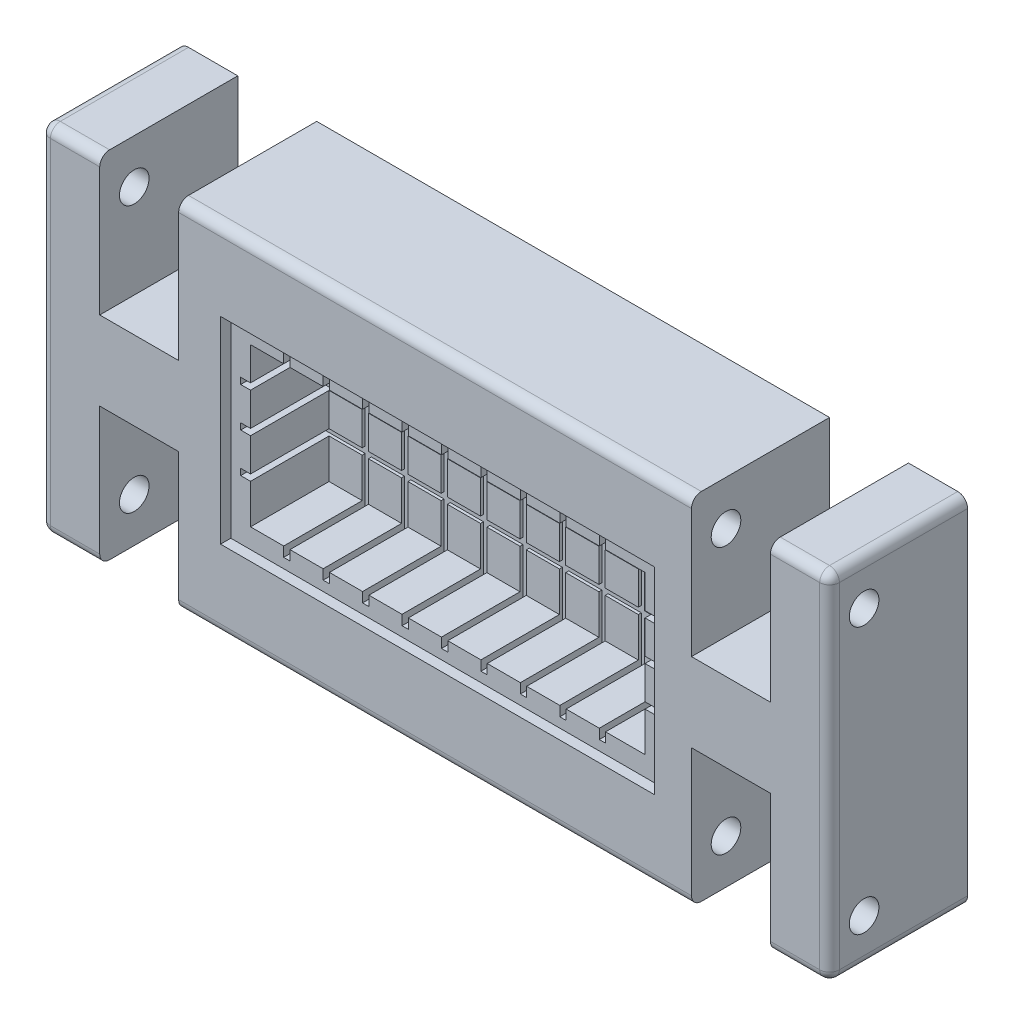
SolidWorks part; units mm, degrees
ref_plane "Alzado" through (0, 0, 0) normal (0, 0, 1) x (1, 0, 0)
ref_plane "Planta" through (0, 0, 0) normal (0, 1, 0) x (1, 0, 0)
ref_plane "Vista lateral" through (0, 0, 0) normal (1, 0, 0) x (0, 0, -1)
sketch "Croquis2" plane through (0, 0, 0) normal (0, 0, 1) x (1, 0, 0)
  line L1 (0, 0) -> (400, 0)
  line L2 (0, 0) -> (0, 180)
  line L3 (0, 180) -> (400, 180)
  line L4 (400, 0) -> (400, 180)
  dimension "D1" = 400
  dimension "D2" = 180
extrude "Saliente-Extruir3" add sketch "Croquis2" along normal blind 70
sketch "Croquis3" plane through (0, 0, 70) normal (0, 0, 1) x (1, 0, 0)
  line L0 (0, 90) -> (400, 90)
  line L1 (0, 180) -> (0, 0) construction
  line L2 (400, 0) -> (400, 180) construction
  line L3 (0, 0) -> (400, 0) construction
  line L4 (30, 0) -> (70, 0)
  line L5 (30, 0) -> (30, 70)
  line L6 (30, 70) -> (70, 70)
  line L7 (70, 0) -> (70, 70)
  line L8 (30, 0) -> (0, 0)
  line L9 (200, 90) -> (200, 0)
  line L10 (370, 0) -> (400, 0)
  line L11 (330, 0) -> (330, 70)
  line L12 (370, 70) -> (330, 70)
  line L13 (370, 0) -> (370, 70)
  line L14 (370, 0) -> (330, 0)
  line L15 (370, 180) -> (330, 180)
  line L16 (370, 180) -> (370, 110)
  line L17 (370, 110) -> (330, 110)
  line L18 (330, 180) -> (330, 110)
  line L19 (370, 180) -> (400, 180)
  line L20 (30, 180) -> (0, 180)
  line L21 (70, 180) -> (70, 110)
  line L22 (30, 110) -> (70, 110)
  line L23 (30, 180) -> (30, 110)
  line L24 (30, 180) -> (70, 180)
  line M9 (0, 0) -> (400, 0)
  line M11 (400, 180) -> (0, 180)
  dimension "D1" = 40
  dimension "D2" = 70
  dimension "D3" = 30
extrude "Cortar-Extruir1" cut sketch "Croquis3" against normal blind 70 contours L23 L22 L21 M11 | L13 L12 L11 M9 | L7 L6 L5 M9 | L16 L17 L18 L15
sketch "Croquis4" plane through (400, 0, 0) normal (1, 0, 0) x (0, 0, -1)
  line L0 (-70, 180) -> (-35, 135) construction
  line L1 (-70, 180) -> (-35, 180) construction
  line L2 (-70, 180) -> (-70, 135) construction
  line L3 (-70, 135) -> (-35, 135) construction
  line L4 (-35, 180) -> (-35, 135) construction
  line L5 (0, 90) -> (-70, 90) construction
  line L6 (0, 0) -> (0, 180) construction
  line L7 (-70, 0) -> (-70, 180) construction
  circle A0 centre (-52.5, 157.5) radius 7.5
  circle A1 centre (-52.5, 22.5) radius 7.5
  dimension "D3" = 15
  dimension "D1" = 45
  dimension "D2" = 35
extrude "Cortar-Extruir2" cut sketch "Croquis4" against normal blind 400
fillet "Redondeo2" radius 5 1 edges at (200, 0, 70)
fillet "Redondeo3" radius 5 1 edges at (200, 180, 70)
fillet "Redondeo4" radius 5 1 edges at (15, 180, 70)
fillet "Redondeo5" radius 5 1 edges at (385, 180, 70)
fillet "Redondeo6" radius 5 1 edges at (385, 0, 70)
fillet "Redondeo7" radius 5 1 edges at (15, 0, 70)
fillet "Redondeo8" radius 5 5 edges at (0, 90, 70) (0, 180, 32.5) (0, 178.5355, 68.5355) (0, 0, 32.5) (0, 1.4645, 68.5355)
fillet "Redondeo9" radius 5 5 edges at (400, 180, 32.5) (400, 178.5355, 68.5355) (400, 90, 70) (400, 0, 32.5) (400, 1.4645, 68.5355)
sketch "Croquis6" plane through (0, 0, 70) normal (0, 0, 1) x (1, 0, 0)
  line L4 (301.25, 130) -> (101.25, 130)
  line L5 (301.25, 130) -> (301.25, 50)
  line L6 (301.25, 50) -> (101.25, 50)
  line L7 (101.25, 130) -> (101.25, 50)
  line L8 (301.25, 130) -> (101.25, 50) construction
  line L9 (301.25, 50) -> (101.25, 130) construction
  point P9 (201.25, 90)
extrude "Cortar-Extruir3" cut sketch "Croquis6" against normal blind 45
sketch "Croquis7" plane through (0, 0, 70) normal (0, 0, 1) x (1, 0, 0)
  line L2 (241.25, 45) -> (238.05, 45)
  line L3 (241.25, 45) -> (241.25, 135)
  line L4 (138.05, 45) -> (141.25, 45)
  line L5 (138.05, 45) -> (138.05, 135)
  line L6 (118.05, 45) -> (121.25, 45)
  line L7 (118.05, 45) -> (118.05, 135)
  line L8 (118.05, 135) -> (121.25, 135)
  line L9 (121.25, 45) -> (121.25, 135)
  line L10 (118.05, 45) -> (121.25, 135) construction
  line L11 (118.05, 135) -> (121.25, 45) construction
  line L12 (138.05, 135) -> (141.25, 135)
  line L13 (141.25, 45) -> (141.25, 135)
  line L14 (138.05, 45) -> (141.25, 135) construction
  line L15 (138.05, 135) -> (141.25, 45) construction
  line L16 (241.25, 135) -> (238.05, 135)
  line L21 (238.05, 45) -> (238.05, 135)
  line L22 (158.05, 45) -> (161.25, 45)
  line L23 (158.05, 45) -> (158.05, 135)
  line L24 (158.05, 135) -> (161.25, 135)
  line L25 (161.25, 45) -> (161.25, 135)
  line L26 (158.05, 45) -> (161.25, 135) construction
  line L27 (158.05, 135) -> (161.25, 45) construction
  line L28 (241.25, 45) -> (238.05, 135) construction
  line L33 (241.25, 135) -> (238.05, 45) construction
  line L34 (178.05, 45) -> (181.25, 45)
  line L35 (178.05, 45) -> (178.05, 135)
  line L36 (178.05, 135) -> (181.25, 135)
  line L37 (181.25, 45) -> (181.25, 135)
  line L38 (178.05, 45) -> (181.25, 135) construction
  line L39 (178.05, 135) -> (181.25, 45) construction
  line L41 (198.05, 45) -> (201.25, 45)
  line L42 (198.05, 45) -> (198.05, 135)
  line L43 (198.05, 135) -> (201.25, 135)
  line L44 (201.25, 45) -> (201.25, 135)
  line L45 (198.05, 45) -> (201.25, 135) construction
  line L46 (198.05, 135) -> (201.25, 45) construction
  line L48 (218.05, 45) -> (221.25, 45)
  line L49 (218.05, 45) -> (218.05, 135)
  line L50 (218.05, 135) -> (221.25, 135)
  line L51 (221.25, 45) -> (221.25, 135)
  line L52 (218.05, 45) -> (221.25, 135) construction
  line L53 (218.05, 135) -> (221.25, 45) construction
  line L54 (261.25, 45) -> (258.05, 45)
  line L55 (261.25, 45) -> (261.25, 135)
  line L56 (261.25, 135) -> (258.05, 135)
  line L57 (258.05, 45) -> (258.05, 135)
  line L58 (261.25, 45) -> (258.05, 135) construction
  line L59 (261.25, 135) -> (258.05, 45) construction
  line L61 (281.25, 45) -> (278.05, 45)
  line L62 (281.25, 45) -> (281.25, 135)
  line L63 (281.25, 135) -> (278.05, 135)
  line L64 (278.05, 45) -> (278.05, 135)
  line L65 (281.25, 45) -> (278.05, 135) construction
  line L66 (281.25, 135) -> (278.05, 45) construction
extrude "Cortar-Extruir4" cut sketch "Croquis7" against normal blind 46.5
sketch "Croquis8" plane through (0, 0, 70) normal (0, 0, 1) x (1, 0, 0)
  line L3 (306.25, 113.2) -> (96.25, 113.2)
  line L4 (306.25, 113.2) -> (306.25, 110)
  line L5 (306.25, 110) -> (96.25, 110)
  line L6 (96.25, 113.2) -> (96.25, 110)
  line L7 (306.25, 113.2) -> (96.25, 110) construction
  line L8 (306.25, 110) -> (96.25, 113.2) construction
  line L10 (306.25, 93.2) -> (96.25, 93.2)
  line L11 (306.25, 93.2) -> (306.25, 90)
  line L12 (306.25, 90) -> (96.25, 90)
  line L13 (96.25, 93.2) -> (96.25, 90)
  line L14 (306.25, 93.2) -> (96.25, 90) construction
  line L15 (306.25, 90) -> (96.25, 93.2) construction
  line L17 (306.25, 73.2) -> (96.25, 73.2)
  line L18 (306.25, 73.2) -> (306.25, 70)
  line L19 (306.25, 70) -> (96.25, 70)
  line L20 (96.25, 73.2) -> (96.25, 70)
  line L21 (306.25, 73.2) -> (96.25, 70) construction
  line L22 (306.25, 70) -> (96.25, 73.2) construction
extrude "Cortar-Extruir5" cut sketch "Croquis8" against normal blind 46.5
sketch "Croquis9" plane through (0, 0, 70) normal (0, 0, 1) x (1, 0, 0)
  line L3 (91.25, 40) -> (311.25, 40)
  line L4 (91.25, 40) -> (91.25, 140)
  line L5 (91.25, 140) -> (311.25, 140)
  line L6 (311.25, 40) -> (311.25, 140)
  line L7 (91.25, 40) -> (311.25, 140) construction
  line L8 (91.25, 140) -> (311.25, 40) construction
  point P8 (201.25, 90)
extrude "Cortar-Extruir6" cut sketch "Croquis9" against normal blind 5.2
